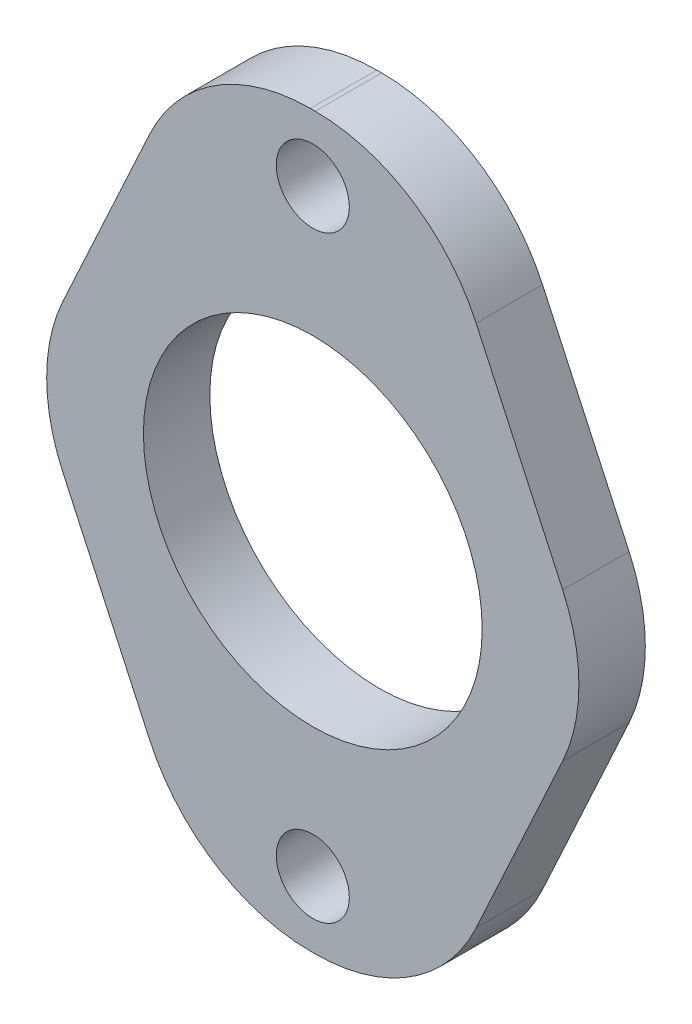
SolidWorks part; units mm, degrees
ref_plane "Plano frontal" through (0, 0, 0) normal (0, 0, 1) x (1, 0, 0)
ref_plane "Plano superior" through (0, 0, 0) normal (0, 1, 0) x (1, 0, 0)
ref_plane "Plano direito" through (0, 0, 0) normal (1, 0, 0) x (0, 0, -1)
sketch "Esboço1" plane through (0, 0, 0) normal (0, 0, 1) x (1, 0, 0)
  line L0 (0, -13.5) -> (0, 13.5) construction
  line L3 (0, 0) -> (7.65, 0) construction
  line L6 (-12.8275, 0) -> (-5.2332, 16.48)
  line L8 (-5.2332, 16.48) -> (5.2332, 16.48)
  line L9 (12.8275, 0) -> (5.2332, 16.48)
  line L10 (12.8275, 0) -> (5.2332, -16.48)
  line L11 (-5.2332, -16.48) -> (5.2332, -16.48)
  line L12 (-12.8275, 0) -> (-5.2332, -16.48)
  line L13 (0, 0) -> (-10.5806, -4.8757) construction
  line L14 (-12.0189, 0) -> (16.4116, 0) construction
  line L15 (-15.0189, 2.75) -> (-12.0189, 2.75) construction
  line L16 (-15.0189, 2.75) -> (-15.0189, -2.75) construction
  line L17 (-15.0189, -2.75) -> (-12.0189, -2.75) construction
  line L18 (-12.0189, 2.75) -> (-12.0189, -2.75) construction
  line L19 (-15.0189, 2.75) -> (-12.0189, -2.75) construction
  line L20 (-15.0189, -2.75) -> (-12.0189, 2.75) construction
  line L21 (15.0189, 1.5) -> (16.4116, 1.5) construction
  line L22 (15.0189, 3) -> (12.0189, 3) construction
  line L23 (15.0189, 3) -> (15.0189, -3) construction
  line L24 (15.0189, -3) -> (12.0189, -3) construction
  line L25 (12.0189, 3) -> (12.0189, -3) construction
  line L26 (15.0189, 3) -> (12.0189, -3) construction
  line L27 (15.0189, -3) -> (12.0189, 3) construction
  line L28 (17.4074, 1.591) -> (0, 0) construction
  circle A1 centre (0, 0) radius 7.65
  circle A2 centre (0, -13.5) radius 1.65
  circle A3 centre (0, 13.5) radius 1.65
  circle A4 centre (0, 13.5) radius 3 construction
  circle A5 centre (0, -13.5) radius 3 construction
  circle A6 centre (0, 0) radius 17.48 construction
  arc A8 (-11.2846, -3.3481) -> (-11.2846, 3.3481) centre (-4.0189, 0) cw construction
  arc A9 (11.2846, -3.3481) -> (11.2846, 3.3481) centre (4.0189, 0) ccw construction
  point P8 (0, 11.85)
  point P10 (0, 7.65)
  point P11 (0, 10.5)
  point P13 (-6.9478, -3.2017)
  point P22 (0, 16.48)
  point P24 (0, 17.48)
  point P28 (-13.5189, 0)
  point P35 (0, -20.7406)
  point P38 (13.5189, 0)
  point P44 (17.4074, 1.591)
  dimension "D1" = 3.3
  dimension "D2" = 15.3
  dimension "D4" = 6
  dimension "D5" = 6
  dimension "D6" = 4
  dimension "D7" = 34.96
  dimension "D8" = 1
  dimension "D9" = 8
  dimension "D3" = 27
  dimension "D10" = 3
  dimension "D11" = 5.5
  dimension "D12" = 6
  dimension "D13" = 3
  dimension "D14" = 1.5
  dimension "D15" = 1
extrude "Ressalto-extrusão1" add sketch "Esboço1" along normal blind 3
fillet "Filete1" radius 8 6 edges at (5.2332, -16.48, 1.5) (-5.2332, -16.48, 1.5) (-5.2332, 16.48, 1.5) (5.2332, 16.48, 1.5) (12.8275, 0, 1.5) (-12.8275, 0, 1.5)
